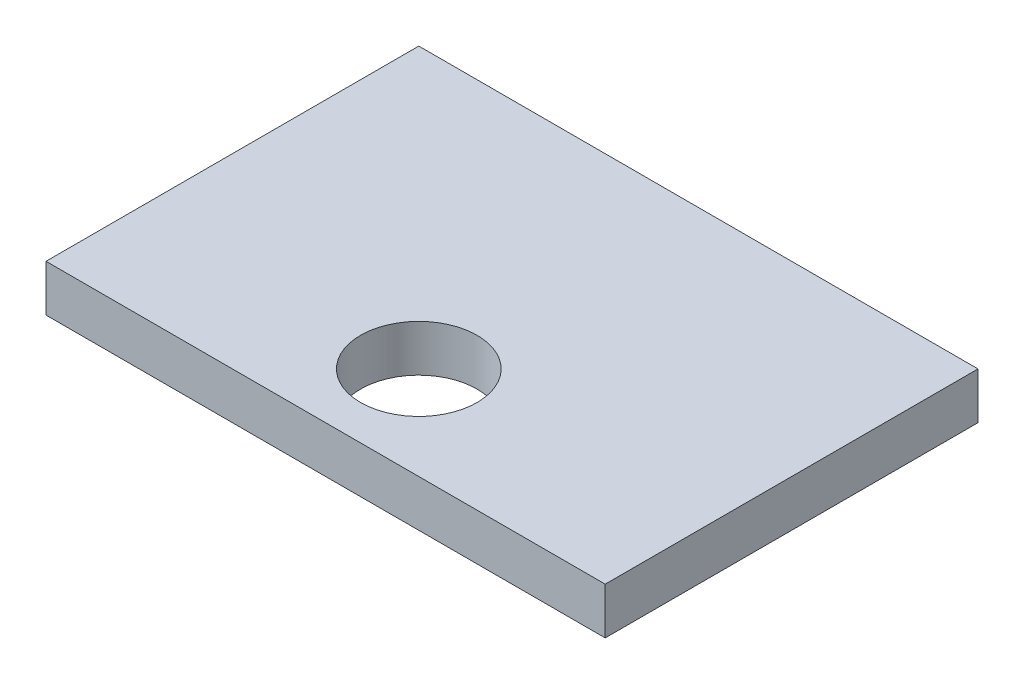
SolidWorks part; units mm, degrees
ref_plane "Plane1" through (0, 0, 0) normal (0, 0, 1) x (1, 0, 0)
ref_plane "Plane2" through (0, 0, 0) normal (0, 1, 0) x (1, 0, 0)
ref_plane "Plane3" through (0, 0, 0) normal (1, 0, 0) x (0, 0, -1)
sketch "Sketch2" plane through (0, 0, 0) normal (0, 1, 0) x (1, 0, 0)
  line L1 (0, 0) -> (120, 0)
  line L2 (0, 0) -> (0, 80)
  line L3 (0, 80) -> (120, 80)
  line L4 (120, 0) -> (120, 80)
  dimension "D1" = 80
  dimension "D2" = 120
extrude "Boss-Extrude1" add sketch "Sketch2" along normal blind 10
sketch "Sketch3" plane through (0, 10, 0) normal (0, 1, 0) x (1, 0, 0)
  line L0 (0, 0) -> (120, 0) construction
  line L1 (120, 0) -> (120, 80) construction
  circle A0 centre (60, 20) radius 12.5
  dimension "D1" = 25
  dimension "D2" = 20
  dimension "D3" = 60
extrude "Cut-Extrude1" cut sketch "Sketch3" against normal blind 10
